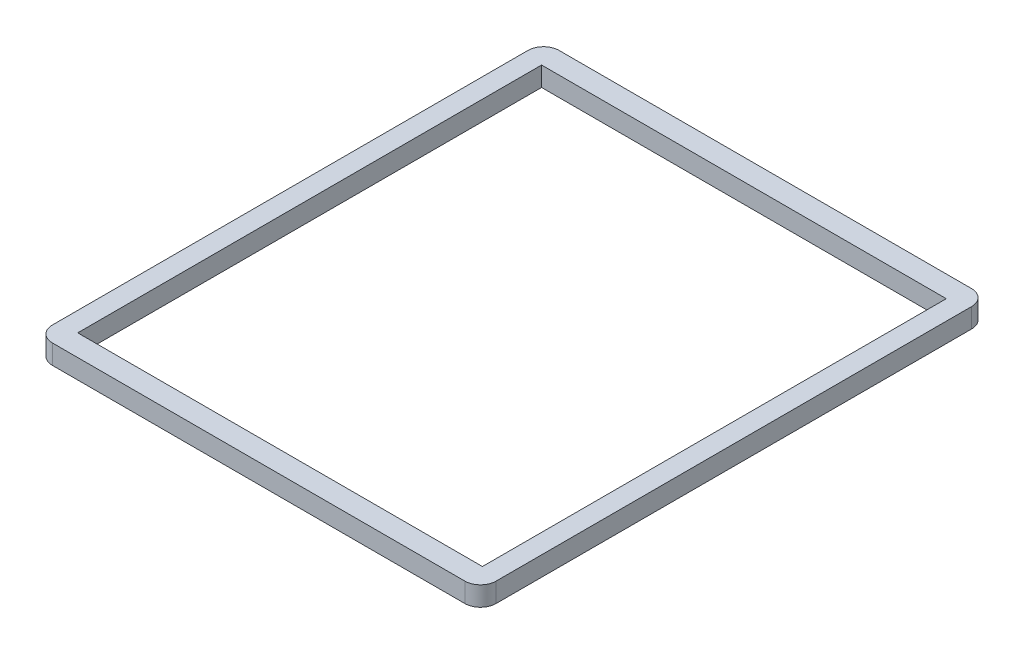
SolidWorks part; units mm, degrees
ref_plane "Front Plane" through (0, 0, 0) normal (0, 0, 1) x (1, 0, 0)
ref_plane "Top Plane" through (0, 0, 0) normal (0, 1, 0) x (1, 0, 0)
ref_plane "Right Plane" through (0, 0, 0) normal (1, 0, 0) x (0, 0, -1)
sketch "Sketch1" plane through (0, 0, 0) normal (0, 1, 0) x (1, 0, 0)
  line L0 (36.195, 41.3385) -> (72.39, 41.3385) construction
  line L1 (2.54, 0) -> (69.85, 0)
  line L2 (0, 2.54) -> (0, 80.137)
  line L3 (2.54, 82.677) -> (69.85, 82.677)
  line L4 (72.39, 2.54) -> (72.39, 80.137)
  line L5 (69.215, 3.4925) -> (3.175, 3.4925)
  line L6 (69.215, 3.4925) -> (69.215, 79.1845)
  line L7 (69.215, 79.1845) -> (3.175, 79.1845)
  line L8 (3.175, 3.4925) -> (3.175, 79.1845)
  line L9 (69.215, 3.4925) -> (3.175, 79.1845) construction
  line L10 (69.215, 79.1845) -> (3.175, 3.4925) construction
  line L11 (72.39, 41.3385) -> (36.195, 41.3385) construction
  line L12 (36.195, 41.3385) -> (36.195, 0) construction
  arc A0 (2.54, 0) -> (0, 2.54) centre (2.54, 2.54) cw
  arc A1 (72.39, 2.54) -> (69.85, 0) centre (69.85, 2.54) cw
  arc A2 (69.85, 82.677) -> (72.39, 80.137) centre (69.85, 80.137) cw
  arc A3 (2.54, 82.677) -> (0, 80.137) centre (2.54, 80.137) ccw
  point P7 (0, 0)
  point P10 (72.39, 0)
  point P15 (0, 82.677)
  point P16 (36.195, 41.3385)
  point P21 (0, 0)
  point P23 (0, 0)
  point P26 (0, 0)
  point P27 (0, 0)
  dimension "D3" = 2.54
  dimension "D1" = 82.677
  dimension "D2" = 72.39
  dimension "D4" = 75.692
  dimension "D5" = 66.04
  dimension "D6" = 3.175
extrude "Boss-Extrude2" add sketch "Sketch1" along normal blind 3.175 contours L2 A3 L3 A2 L4 A1 L1 A0
